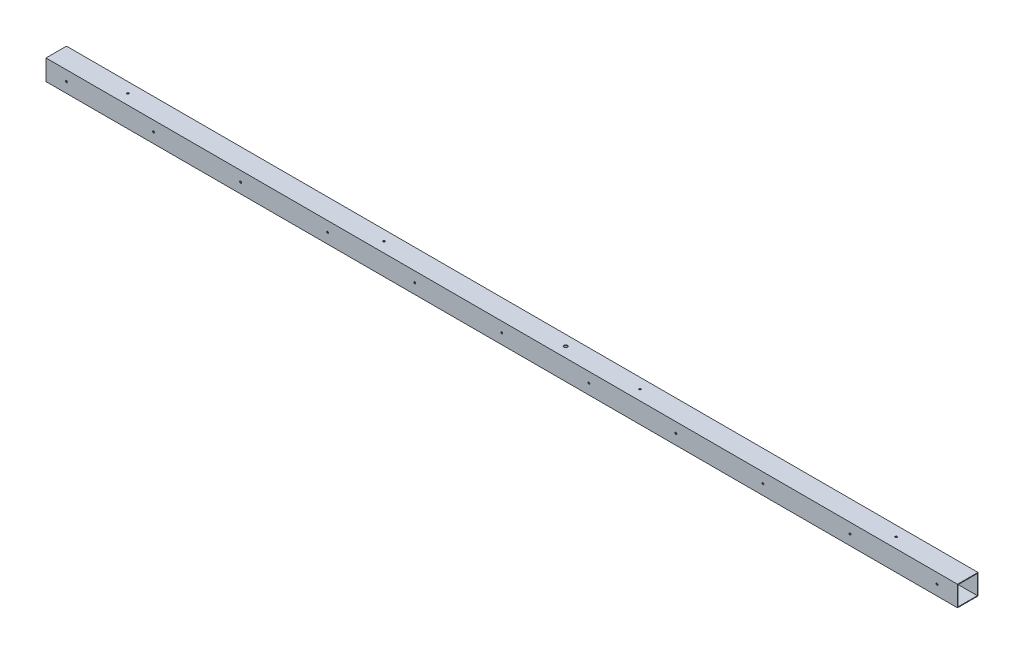
SolidWorks part; units mm, degrees
ref_plane "Front Plane" through (0, 0, 0) normal (0, 0, 1) x (1, 0, 0)
ref_plane "Top Plane" through (0, 0, 0) normal (0, 1, 0) x (1, 0, 0)
ref_plane "Right Plane" through (0, 0, 0) normal (1, 0, 0) x (0, 0, -1)
sketch "Sketch1" plane through (0, 0, 0) normal (1, 0, 0) x (0, 0, -1)
  line L0 (1.5875, 1.5875) -> (1.5875, 49.2125)
  line L1 (0, 0) -> (50.8, 0)
  line L2 (0, 0) -> (0, 50.8)
  line L3 (0, 50.8) -> (50.8, 50.8)
  line L4 (50.8, 0) -> (50.8, 50.8)
  line L5 (1.5875, 49.2125) -> (49.2125, 49.2125)
  line L6 (49.2125, 1.5875) -> (49.2125, 49.2125)
  line L7 (1.5875, 1.5875) -> (49.2125, 1.5875)
  dimension "D2" = 50.8
  dimension "D1" = 1.5875
extrude "Boss-Extrude1" add sketch "Sketch1" along normal blind 2260.6
sketch "Sketch3" plane through (0, 0, -50.8) normal (0, 0, -1) x (-1, 0, 0)
  line L0 (0, 0) -> (0, 50.8) construction
  line L1 (-2260.6, 50.8) -> (0, 50.8) construction
  circle A0 centre (-50.8, 25.4) radius 2.3812
  dimension "D3" = 4.7625
  dimension "D1" = 50.8
  dimension "D2" = 25.4
extrude "Cut-Extrude2" cut sketch "Sketch3" against normal through all
pattern_linear "LPattern2" count 11 spacing 215.9 along (1, 0, 0) of "Cut-Extrude2"
sketch "Sketch4" plane through (0, 0, 0) normal (0, -1, 0) x (1, 0, 0)
  line L3 (0, 0) -> (0, -50.8) construction
  circle A3 centre (177.8, -25.4) radius 2.3813
  point P16 (0, -25.4)
  dimension "D1" = 177.8
  dimension "D4" = 4.7625
extrude "Cut-Extrude3" cut sketch "Sketch4" against normal up to surface (50.8 mm away) up to face at (1130.3, 50.8, -25.4)
pattern_linear "LPattern3" count 4 spacing 635 along (1, 0, 0) of "Cut-Extrude3"
sketch "Sketch5" plane through (0, 0, 0) normal (0, -1, 0) x (1, 0, 0)
  line L0 (2260.6, 0) -> (2260.6, -50.8) construction
  circle A0 centre (1263.65, -25.4) radius 4.445
  point P5 (2260.6, -25.4)
  dimension "D2" = 8.89
  dimension "D1" = 996.95
extrude "Cut-Extrude4" cut sketch "Sketch5" against normal through all
